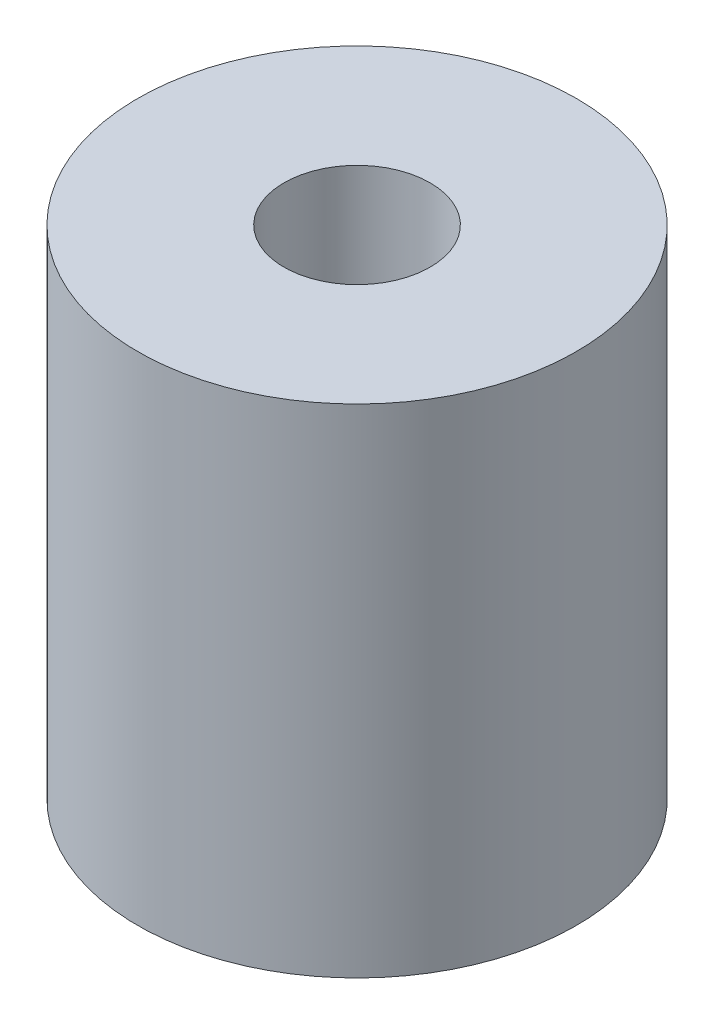
SolidWorks part; units mm, degrees
ref_plane "Front Plane" through (0, 0, 0) normal (0, 0, 1) x (1, 0, 0)
ref_plane "Top Plane" through (0, 0, 0) normal (0, 1, 0) x (1, 0, 0)
ref_plane "Right Plane" through (0, 0, 0) normal (1, 0, 0) x (0, 0, -1)
sketch "Sketch1" plane through (0, 0, 0) normal (0, 0, 1) x (1, 0, 0)
  line L0 (9.525, 21.59) -> (3.175, 21.59)
  line L1 (3.175, 21.59) -> (3.175, 0)
  line L2 (3.175, 0) -> (9.525, 0)
  line L3 (9.525, 0) -> (9.525, 21.59)
  line L4 (0, 21.59) -> (0, 0) construction
revolve "Revolve1" add sketch "Sketch1" angle 360 about L4
